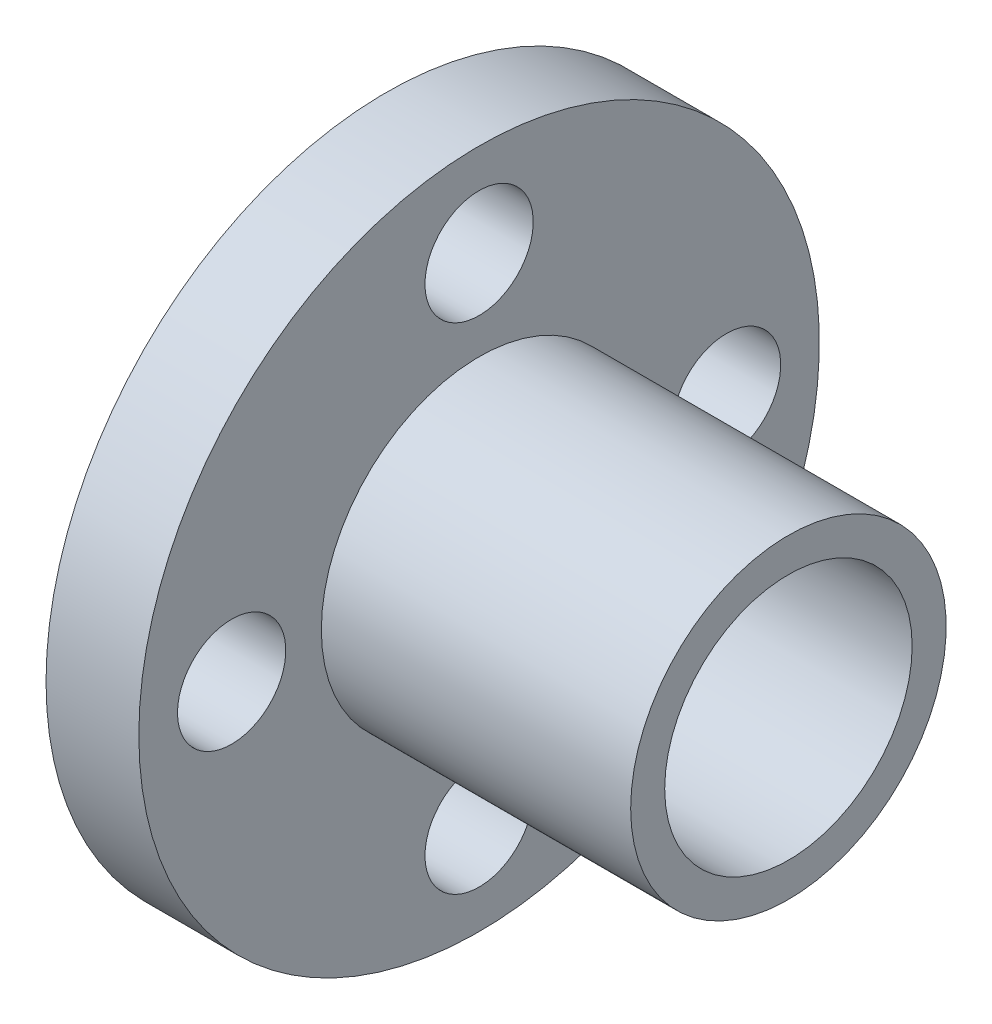
SolidWorks part; units mm, degrees
ref_plane "Front Plane" through (0, 0, 0) normal (0, 0, 1) x (1, 0, 0)
ref_plane "Top Plane" through (0, 0, 0) normal (0, 1, 0) x (1, 0, 0)
ref_plane "Right Plane" through (0, 0, 0) normal (1, 0, 0) x (0, 0, -1)
sketch "Sketch1" plane through (0, 0, 0) normal (0, 0, 1) x (1, 0, 0)
  line L0 (-5.75, -5.1) -> (-5.75, -11)
  line L1 (-7.25, -4) -> (-7.25, -5.1)
  line L2 (-2.75, -5.1) -> (-2.75, -11)
  line L3 (7.25, -4) -> (7.25, -5.1)
  line L4 (-7.25, -5.1) -> (-5.75, -5.1)
  line L5 (-2.75, -5.1) -> (7.25, -5.1)
  line L6 (-5.75, -11) -> (-2.75, -11)
  line L7 (-7.25, -4) -> (7.25, -4)
  line L8 (-7.25, 0) -> (7.25, 0) construction
revolve "Revolve1" add sketch "Sketch1" angle 360 about L8
sketch "Sketch3" plane through (-5.75, 0, 0) normal (-1, 0, 0) x (0, 0, 1)
  line L3 (5205.1784, 2346.7456) -> (5205.1784, 2340.8456)
  line L4 (5203.6784, 2347.8456) -> (5203.6784, 2346.7456)
  line L5 (5208.1784, 2346.7456) -> (5208.1784, 2340.8456)
  line L6 (5218.1784, 2347.8456) -> (5218.1784, 2346.7456)
  line L7 (5203.6784, 2346.7456) -> (5205.1784, 2346.7456)
  line L8 (5208.1784, 2346.7456) -> (5218.1784, 2346.7456)
  line L9 (5205.1784, 2340.8456) -> (5208.1784, 2340.8456)
  line L10 (5203.6784, 2347.8456) -> (5218.1784, 2347.8456)
  line L11 (5203.6784, 2351.8456) -> (5218.1784, 2351.8456) construction
  circle A0 centre (0, 8) radius 1.75
  circle A1 centre (0, -8) radius 1.75
  circle A2 centre (8, 0) radius 1.75
  circle A3 centre (-8, 0) radius 1.75
extrude "Cut-Extrude2" cut sketch "Sketch3" against normal blind 3
